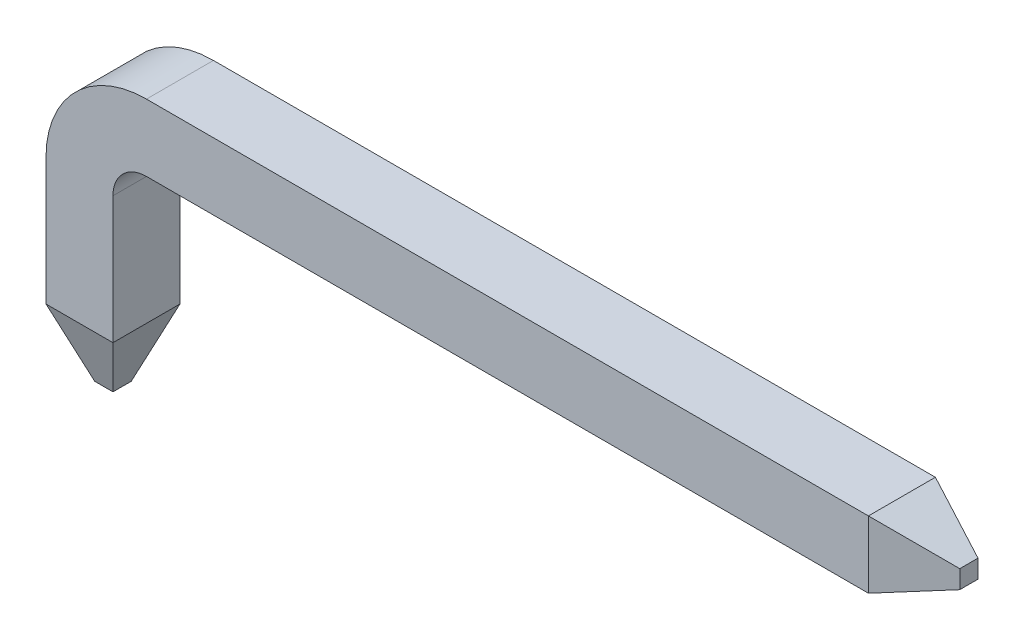
SolidWorks part; units mm, degrees
ref_plane "Front Plane" through (0, 0, 0) normal (0, 0, 1) x (1, 0, 0)
ref_plane "Top Plane" through (0, 0, 0) normal (0, 1, 0) x (1, 0, 0)
ref_plane "Right Plane" through (0, 0, 0) normal (1, 0, 0) x (0, 0, -1)
sketch "Sketch1" plane through (0, 0, 0) normal (0, 1, 0) x (1, 0, 0)
  line L1 (0, 0) -> (0.5, 0)
  line L2 (0, 0) -> (0, 0.5)
  line L3 (0, 0.5) -> (0.5, 0.5)
  line L4 (0.5, 0) -> (0.5, 0.5)
sketch "Sketch2" plane through (0, 0, 0) normal (0, 0, 1) x (1, 0, 0)
  line L0 (0, 0) -> (0.5, 0) construction
  line L1 (0.25, 0) -> (0.25, 1.45) construction
  line L2 (0.25, 1.45) -> (6.14, 1.45) construction
  line L3 (0.25, 0) -> (0.25, 0.95)
  line L4 (0.75, 1.45) -> (6.14, 1.45)
  line L5 (0.25, 0) -> (0.75, 0) construction
  line L6 (0.75, 0) -> (0.75, 1.45) construction
  line L7 (0.75, 0.95) -> (0.25, 0.95) construction
  arc A0 (0.25, 0.95) -> (0.75, 1.45) centre (0.75, 0.95) cw
sweep "Sweep4" add profiles "Sketch1" path "Sketch2"
sketch "Sketch6" plane through (6.14, 0, 0) normal (1, 0, 0) x (0, 0, -1)
  line L1 (0, 1.7) -> (0.5, 1.7)
  line L2 (0, 1.7) -> (0, 1.2)
  line L3 (0, 1.2) -> (0.5, 1.2)
  line L4 (0.5, 1.7) -> (0.5, 1.2)
extrude "Boss-Extrude1" add sketch "Sketch6" along normal blind 0.5 draft 20
sketch "Sketch7" plane through (0, 0, 0) normal (0, -1, 0) x (1, 0, 0)
  line L1 (0, 0) -> (0.5, 0)
  line L2 (0, 0) -> (0, -0.5)
  line L3 (0, -0.5) -> (0.5, -0.5)
  line L4 (0.5, 0) -> (0.5, -0.5)
extrude "Boss-Extrude2" add sketch "Sketch7" along normal blind 0.5 draft 20
ref_plane "Plane1" through (0, 2.45, 0) normal (0, 1, 0) x (-1, 0, 0)
